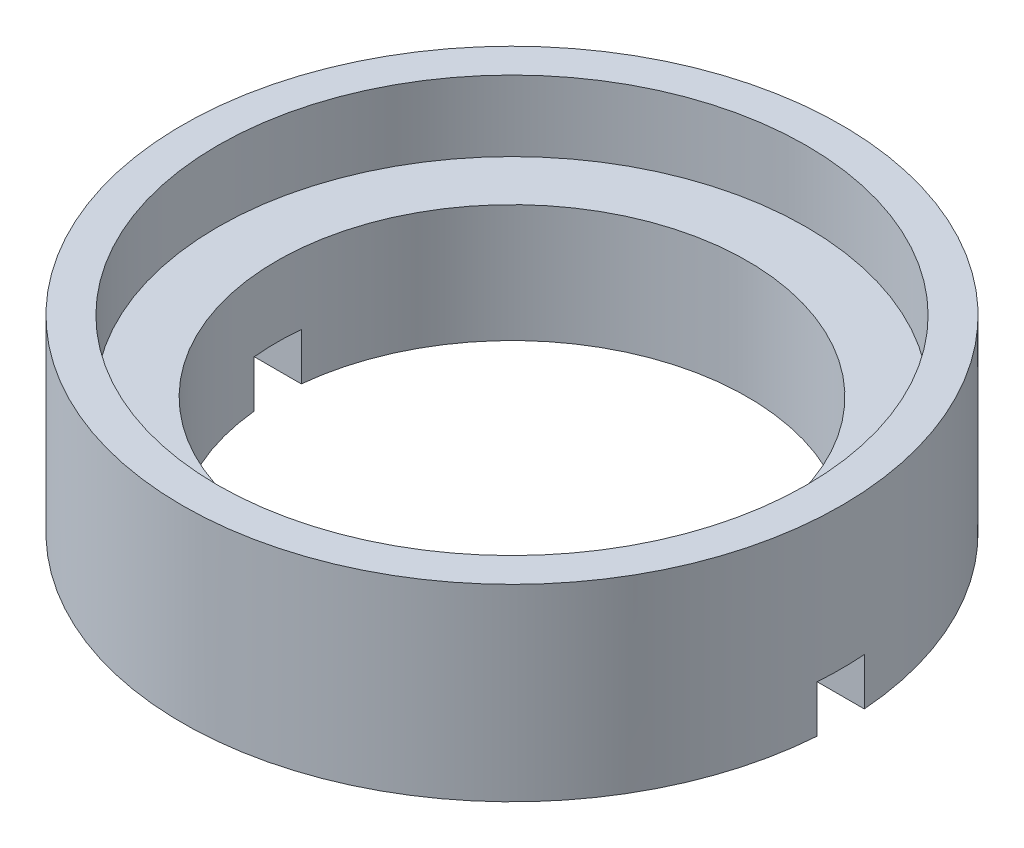
SolidWorks part; units mm, degrees
ref_plane "Front Plane" through (0, 0, 0) normal (0, 0, 1) x (1, 0, 0)
ref_plane "Top Plane" through (0, 0, 0) normal (0, 1, 0) x (1, 0, 0)
ref_plane "Right Plane" through (0, 0, 0) normal (1, 0, 0) x (0, 0, -1)
sketch "Sketch1" plane through (0, 0, 0) normal (0, 1, 0) x (1, 0, 0)
  circle A0 centre (0, 0) radius 7
  dimension "D1" = 14
extrude "Boss-Extrude1" add sketch "Sketch1" along normal blind 4
sketch "Sketch2" plane through (0, 4, 0) normal (0, 1, 0) x (1, 0, 0)
  circle A0 centre (0, 0) radius 6.25
  dimension "D1" = 12.5
extrude "Cut-Extrude1" cut sketch "Sketch2" against normal blind 1.5
sketch "Sketch3" plane through (0, 0, 0) normal (0, -1, 0) x (1, 0, 0)
  circle A0 centre (0, 0) radius 5
  dimension "D1" = 10
extrude "Cut-Extrude2" cut sketch "Sketch3" against normal through all
cosmetic thread "Cosmetic Thread1" parameters "D2"=11
sketch "Sketch4" plane through (0, 0, 0) normal (0, -1, 0) x (1, 0, 0)
  line L1 (-8, -0.5) -> (8, -0.5)
  line L2 (-8, -0.5) -> (-8, 0.5)
  line L3 (-8, 0.5) -> (8, 0.5)
  line L4 (8, -0.5) -> (8, 0.5)
  line L5 (-8, -0.5) -> (8, 0.5) construction
  line L6 (-8, 0.5) -> (8, -0.5) construction
  circle A2 centre (0, 0) radius 7 construction
  point P0 (0, 0)
  dimension "D1" = 1
  dimension "D2" = 1
extrude "Cut-Extrude3" cut sketch "Sketch4" against normal blind 1
